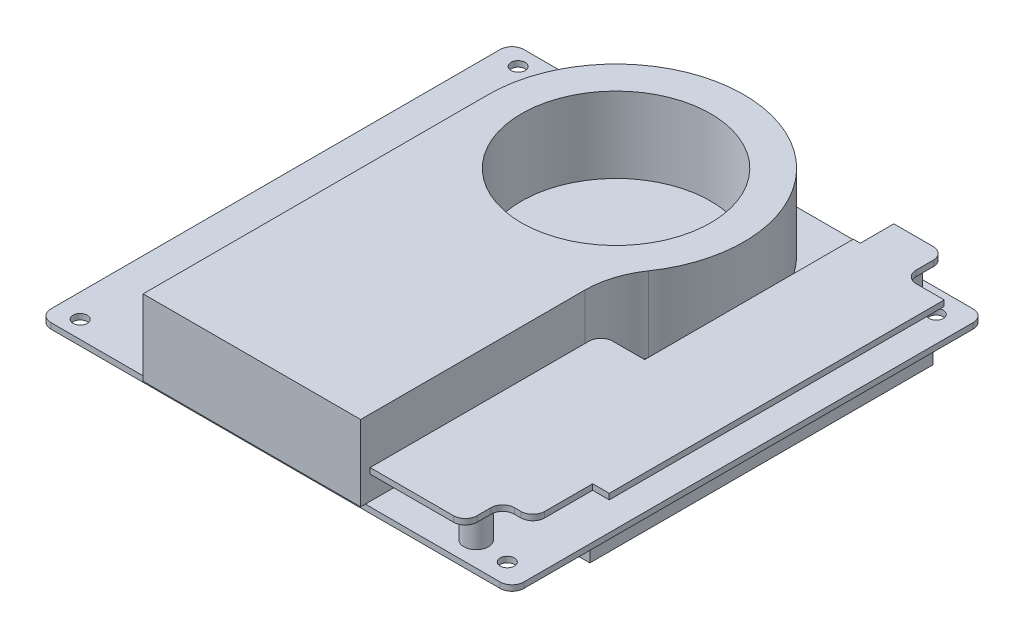
SolidWorks part; units mm, degrees
ref_plane "Front Plane" through (0, 0, 0) normal (0, 0, 1) x (1, 0, 0)
ref_plane "Top Plane" through (0, 0, 0) normal (0, 1, 0) x (1, 0, 0)
ref_plane "Right Plane" through (0, 0, 0) normal (1, 0, 0) x (0, 0, -1)
sketch "Sketch1" plane through (0, 0, 0) normal (0, 1, 0) x (1, 0, 0)
  line L1 (2.5, 100) -> (97.5, 100)
  line L2 (0, 97.5) -> (0, 2.5)
  line L3 (2.5, 0) -> (97.5, 0)
  line L4 (100, 97.5) -> (100, 2.5)
  circle A0 centre (5, 96.3) radius 1.5
  circle A1 centre (94.6, 95.1) radius 1.5
  circle A2 centre (5, 3.7) radius 1.5
  circle A3 centre (94.6, 4.4) radius 1.5
  arc A4 (97.5, 0) -> (100, 2.5) centre (97.5, 2.5) ccw
  arc A5 (0, 2.5) -> (2.5, 0) centre (2.5, 2.5) ccw
  arc A6 (2.5, 100) -> (0, 97.5) centre (2.5, 97.5) ccw
  arc A7 (97.5, 100) -> (100, 97.5) centre (97.5, 97.5) cw
  point P17 (0, 0)
  dimension "D1" = 3
  dimension "D12" = 2.5
  dimension "D2" = 100
  dimension "D3" = 100
  dimension "D4" = 3.7
  dimension "D5" = 5
  dimension "D6" = 5
  dimension "D7" = 3.7
  dimension "D8" = 4.9
  dimension "D9" = 5.4
  dimension "D10" = 5.4
  dimension "D11" = 4.4
extrude "Boss-Extrude1" add sketch "Sketch1" along normal blind 1.2
sketch "Sketch2" plane through (0, 0, 0) normal (0, -1, 0) x (1, 0, 0)
  line L1 (22.0626, -21.8322) -> (51.9036, -21.8322)
  line L2 (22.0626, -21.8322) -> (22.0626, -76.5975)
  line L3 (22.0626, -76.5975) -> (51.9036, -76.5975)
  line L4 (51.9036, -21.8322) -> (51.9036, -76.5975)
extrude "Boss-Extrude2" add sketch "Sketch2" along normal blind 7
sketch "Sketch3" plane through (0, 0, 0) normal (0, -1, 0) x (1, 0, 0)
  line L1 (96.8017, -19.6647) -> (63.0137, -19.6647)
  line L2 (96.8017, -19.6647) -> (96.8017, -92.2461)
  line L3 (96.8017, -92.2461) -> (63.0137, -92.2461)
  line L4 (63.0137, -19.6647) -> (63.0137, -92.2461)
extrude "Boss-Extrude3" add sketch "Sketch3" along normal blind 5.5
sketch "Sketch4" plane through (0, 1.2, 0) normal (0, 1, 0) x (1, 0, 0)
  line L0 (23, -1) -> (23, 72)
  line L1 (69, 46.3875) -> (69, -1)
  line L2 (69, -1) -> (23, -1)
  line L3 (2.5, 0) -> (97.5, 0) construction
  line L4 (0, 97.5) -> (0, 2.5) construction
  arc A0 (23, 72) -> (72.2, 56.6325) centre (50, 72) cw
  arc A1 (72.2, 56.6325) -> (69, 46.3875) centre (87, 46.3875) ccw
  circle A2 centre (50, 72) radius 20
  dimension "D6" = 18
  dimension "D7" = 40
  dimension "D1" = 1
  dimension "D2" = 46
  dimension "D3" = 23
  dimension "D4" = 72
  dimension "D5" = 27
extrude "Boss-Extrude4" add sketch "Sketch4" along normal blind 16
sketch "Sketch5" plane through (0, 1.2, 0) normal (0, 1, 0) x (1, 0, 0)
  circle A0 centre (87.842, 95.2879) radius 2.6
  circle A1 centre (87.2269, 5.2013) radius 2.6
  dimension "D1" = 5.2
extrude "Boss-Extrude5" add sketch "Sketch5" along normal blind 6
sketch "Sketch6" plane through (0, 7.2, 0) normal (0, 1, 0) x (1, 0, 0)
  line L0 (80.7398, 100) -> (80.7398, 92.9072)
  line L1 (80.7398, 92.9072) -> (79.2669, 92.9072)
  line L2 (79.2669, 92.9072) -> (79.2669, 48.7857)
  line L3 (79.2669, 48.7857) -> (70, 48.7857)
  line L4 (70, 48.7857) -> (70, 0)
  line L5 (69, 0) -> (97.5, 0) construction
  line L6 (70, 0) -> (90.1178, 0)
  line L7 (90.1178, 0) -> (90.1178, 7.9178)
  line L8 (90.1178, 7.9178) -> (96.4881, 7.9178)
  line L9 (96.4881, 7.9178) -> (96.4881, 20.5565)
  line L10 (96.4881, 20.5565) -> (100, 20.5565)
  line L11 (100, 2.5) -> (100, 97.5) construction
  line L12 (100, 20.5565) -> (100, 91.3871)
  line L13 (100, 91.3871) -> (91.5681, 91.3871)
  line L14 (91.5681, 91.3871) -> (91.5681, 100)
  line L15 (97.5, 100) -> (2.5, 100) construction
  line L16 (91.5681, 100) -> (80.7398, 100)
extrude "Boss-Extrude6" add sketch "Sketch6" along normal blind 1.2
fillet "Fillet1" radius 2.5 6 edges at (70, 7.8, -48.7857) (91.5681, 7.8, -100) (91.5681, 7.8, -91.3871) (96.4881, 7.8, -7.9178) (90.1178, 7.8, -7.9178) (90.1178, 7.8, 0)
